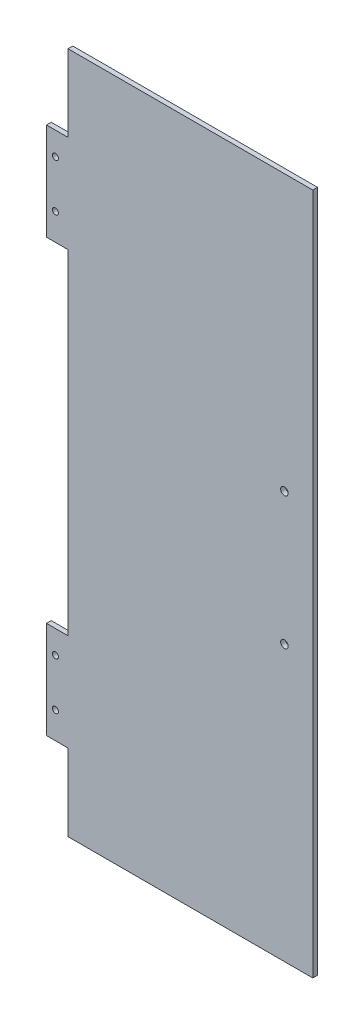
SolidWorks part; units mm, degrees
ref_plane "Front Plane" through (0, 0, 0) normal (0, 0, 1) x (1, 0, 0)
ref_plane "Top Plane" through (0, 0, 0) normal (0, 1, 0) x (1, 0, 0)
ref_plane "Right Plane" through (0, 0, 0) normal (1, 0, 0) x (0, 0, -1)
sketch "Sketch1" plane through (0, 0, 0) normal (0, 0, 1) x (1, 0, 0)
  line L0 (-164.338, 229.108) -> (0, 229.108) construction
  line L1 (0, 0) -> (-164.338, 0)
  line L2 (0, 0) -> (0, 458.216)
  line L3 (0, 458.216) -> (-164.338, 458.216)
  line L4 (-164.338, 0) -> (-164.338, 458.216)
  line L5 (-82.169, 458.216) -> (-82.169, 0) construction
  line L6 (-164.338, 116.84) -> (-178.816, 116.84)
  line L7 (-164.338, 51.562) -> (-178.816, 51.562)
  line L8 (-178.816, 116.84) -> (-178.816, 51.562)
  line L9 (-303.3951, 65.151) -> (-302.9884, 65.151)
  line L10 (-164.338, 406.654) -> (-178.816, 406.654)
  line L11 (-164.338, 341.376) -> (-178.816, 341.376)
  line L12 (-178.816, 341.376) -> (-178.816, 406.654)
  line L13 (-164.338, 341.376) -> (-164.338, 406.654)
  dimension "D1" = 458.216
  dimension "D2" = 164.338
  dimension "D3" = 51.562
  dimension "D4" = 65.278
  dimension "D5" = 14.478
extrude "Boss-Extrude3" add sketch "Sketch1" along normal blind 3.175 contours L4 L1 L2 L3 | L6 L8 L7 L4 | L13 L10 L12 L11
sketch "Sketch2" plane through (0, 0, 3.175) normal (0, 0, 1) x (1, 0, 0)
  line L0 (-164.338, 229.108) -> (0, 229.108) construction
  line L1 (-164.338, 116.84) -> (-164.338, 341.376) construction
  line L2 (0, 0) -> (0, 458.216) construction
  line L3 (-178.816, 116.84) -> (-178.816, 51.562) construction
  line L4 (-164.338, 51.562) -> (-178.816, 51.562) construction
  line L5 (-164.338, 116.84) -> (-178.816, 116.84) construction
  line L6 (-164.338, 341.376) -> (-178.816, 341.376) construction
  line L7 (-164.338, 406.654) -> (-178.816, 406.654) construction
  line L8 (-178.816, 341.376) -> (-178.816, 406.654) construction
  circle A0 centre (-172.8149, 69.4938) radius 2.032
  circle A1 centre (-172.8149, 101.2438) radius 2.032
  circle A2 centre (-172.8149, 391.16) radius 2.032
  circle A3 centre (-172.8149, 359.41) radius 2.032
  dimension "D1" = 4.064
  dimension "D2" = 4.064
  dimension "D3" = 31.75
  dimension "D4" = 6.0011
  dimension "D5" = 17.9318
  dimension "D6" = 15.5962
  dimension "D8" = 15.494
  dimension "D9" = 31.75
  dimension "D10" = 6.0011
  dimension "D11" = 4.064
  dimension "D12" = 4.064
  dimension "D7" = 18.034
extrude "Cut-Extrude1" cut sketch "Sketch2" against normal through all
sketch "Sketch4" plane through (0, 0, 3.175) normal (0, 0, 1) x (1, 0, 0)
  line L0 (-210.832, 229.0858) -> (93.968, 229.0858) construction
  line L1 (-210.832, 495.7858) -> (-210.832, -37.6142) construction
  line L2 (93.968, -37.6142) -> (93.968, 495.7858) construction
  line L3 (-19.05, 184.6358) -> (-19.05, 273.5358) construction
  line L4 (0, 0) -> (0, 458.216) construction
  circle A0 centre (-19.05, 184.6358) radius 2.54
  circle A1 centre (-19.05, 273.5358) radius 2.54
  point P8 (-19.05, 229.0858)
  dimension "D2" = 19.05
  dimension "D3" = 5.08
  dimension "D4" = 5.08
  dimension "D1" = 88.9
extrude "Cut-Extrude3" cut sketch "Sketch4" against normal through all
